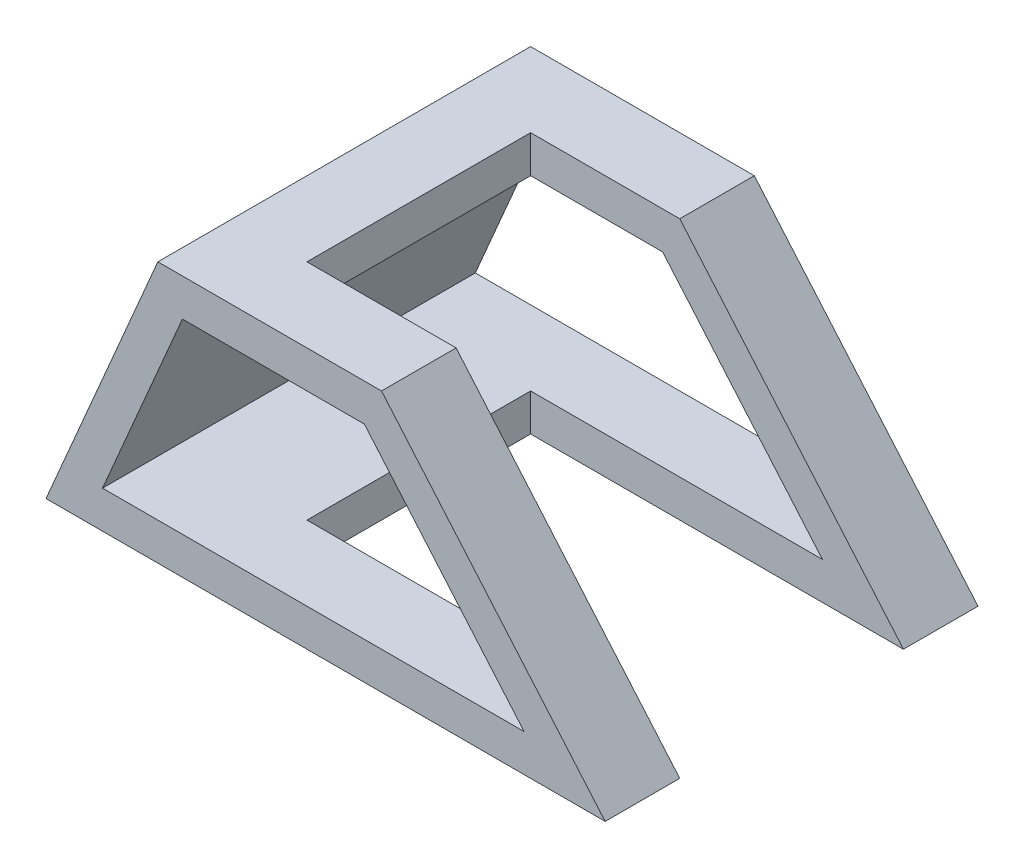
SolidWorks part; units mm, degrees
material "AISI 1020"
ref_plane "Plan de face" through (0, 0, 0) normal (0, 0, 1) x (1, 0, 0)
ref_plane "Plan de dessus" through (0, 0, 0) normal (0, 1, 0) x (1, 0, 0)
ref_plane "Plan de droite" through (0, 0, 0) normal (1, 0, 0) x (0, 0, -1)
sketch "Esquisse4" plane through (0, 0, 0) normal (0, 0, 1) x (1, 0, 0)
  line L0 (30, 70) -> (0, 0)
  line L1 (30, 0) -> (90, 0)
  line L3 (30, 70) -> (90, 70)
  line L5 (0, 0) -> (30, 0)
  line L6 (90, 70) -> (150, 0)
  line L7 (150, 0) -> (90, 0)
  dimension "D1" = 70
  dimension "D2" = 60
  dimension "D3" = 30
  dimension "D4" = 60
extrude "Extru.-Mince5" add sketch "Esquisse4" against normal blind 100 thin thin type one direction reverse wall 10
sketch "Esquisse8" plane through (0, 70, 0) normal (0, 1, 0) x (1, 0, 0)
  line L1 (50, 80) -> (150, 80)
  line L2 (50, 80) -> (50, 20)
  line L3 (50, 20) -> (150, 20)
  line L4 (150, 80) -> (150, 20)
  dimension "D1" = 20
  dimension "D2" = 100
  dimension "D3" = 20
  dimension "D4" = 20
extrude "Enlèv. mat.-Extru.4" cut sketch "Esquisse8" against normal through all
